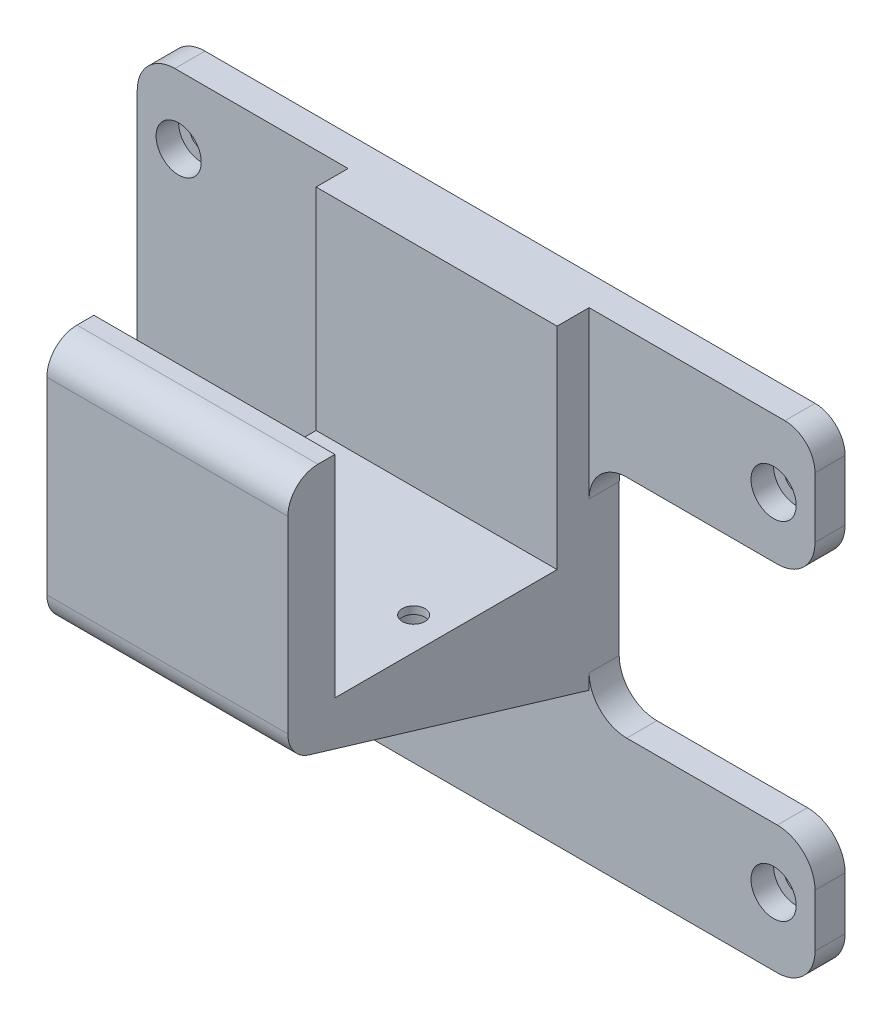
SolidWorks part; units mm, degrees
ref_plane "前视基准面" through (0, 0, 0) normal (0, 0, 1) x (1, 0, 0)
ref_plane "上视基准面" through (0, 0, 0) normal (0, 1, 0) x (1, 0, 0)
ref_plane "右视基准面" through (0, 0, 0) normal (1, 0, 0) x (0, 0, -1)
sketch "草图1" plane through (0, 0, 0) normal (0, 0, 1) x (1, 0, 0)
  line L0 (0, 0) -> (44.2288, 0) construction
  line L1 (-40, 32) -> (41, 32)
  line L2 (-45, 27) -> (-45, -27)
  line L3 (-40, -32) -> (40, -32)
  line L5 (-45, 32) -> (45, -32) construction
  line L6 (-45, -32) -> (45, 32) construction
  line L7 (0, 0) -> (0, 17.8738) construction
  line L8 (45, -20) -> (45, -27)
  line L9 (40, 15) -> (20, 15)
  line L11 (40, -15) -> (20, -15)
  line L12 (15, 10) -> (15, -10)
  line L13 (45, 28) -> (45, 20)
  arc A1 (40, -32) -> (45, -27) centre (40, -27) ccw
  arc A2 (-45, -27) -> (-40, -32) centre (-40, -27) ccw
  arc A3 (-40, 32) -> (-45, 27) centre (-40, 27) ccw
  circle A4 centre (-39.5, 23) radius 1.5
  circle A5 centre (-39.5, -23) radius 1.5
  circle A6 centre (39.5, -23) radius 1.5
  circle A7 centre (39.5, 23) radius 1.5
  arc A8 (45, -20) -> (40, -15) centre (40, -20) ccw
  arc A9 (20, -15) -> (15, -10) centre (20, -10) cw
  arc A10 (20, 15) -> (15, 10) centre (20, 10) ccw
  arc A11 (40, 15) -> (45, 20) centre (40, 20) ccw
  arc A12 (41, 32) -> (45, 28) centre (41, 28) cw
  point P39 (15, 15)
  point P42 (45, 15)
  dimension "D3" = 4
  dimension "D4" = 46
  dimension "D9" = 5
  dimension "D1" = 64
  dimension "D2" = 90
  dimension "D6" = 15
  dimension "D7" = 15
  dimension "D8" = 30
extrude "凸台-拉伸1" add sketch "草图1" along normal blind 4
sketch "草图2" plane through (0, 0, 4) normal (0, 0, 1) x (1, 0, 0)
  line L0 (0, 0) -> (-52.5196, 0) construction
  line L1 (0, 0) -> (0, 42.2378) construction
  circle A0 centre (-39.5, 23) radius 3
  circle A1 centre (-39.5, -23) radius 3
  circle A2 centre (39.5, -23) radius 3
  circle A3 centre (39.5, 23) radius 3
extrude "切除-拉伸1" cut sketch "草图2" against normal blind 3
sketch "草图3" plane through (0, 0, 4) normal (0, 0, 1) x (1, 0, 0)
  line L1 (-17, 32) -> (15, 32)
  line L2 (-17, 32) -> (-17, -12)
  line L3 (-17, -12) -> (15, -12)
  line L4 (15, 32) -> (15, -12)
  line L9 (15, -10) -> (15, 10) construction
  line L10 (41, 32) -> (-40, 32) construction
  dimension "D1" = 32
extrude "凸台-拉伸2" add sketch "草图3" along normal blind 40
sketch "草图4" plane through (0, 32, 0) normal (0, 1, 0) x (1, 0, 0)
  line L0 (-15, -23) -> (19.2476, -23) construction
  line L1 (-17, -44) -> (-17, -4) construction
  circle A0 centre (-13, -13) radius 1.5
  circle A1 centre (-13, -33) radius 1.5
  circle A2 centre (10.7, -23) radius 1.5
  dimension "D1" = 20
  dimension "D2" = 23.7
  dimension "D3" = 4
extrude "切除-拉伸2" cut sketch "草图4" against normal through all
sketch "草图5" plane through (0, -12, 0) normal (0, -1, 0) x (1, 0, 0)
  circle A0 centre (-13, 33) radius 3
  circle A1 centre (-13, 13) radius 3
  circle A2 centre (10.7, 23) radius 3
extrude "切除-拉伸10" cut sketch "草图5" against normal blind 15
sketch "草图7" plane through (0, 32, 0) normal (0, 1, 0) x (1, 0, 0)
  line L0 (-17, -44) -> (-17, -4) construction
  line L1 (-17, -8.25) -> (15, -8.25)
  line L2 (-17, -8.25) -> (-17, -37.75)
  line L3 (-17, -37.75) -> (15, -37.75)
  line L4 (15, -8.25) -> (15, -37.75)
  line L5 (15, -44) -> (15, -4) construction
  line L6 (10.7, -23) -> (-18.4544, -23) construction
  line L7 (-17, -4) -> (-40, -4) construction
  dimension "D1" = 4.25
extrude "切除-拉伸12" cut sketch "草图7" against normal blind 28
sketch "草图6" plane through (-17, 0, 0) normal (-1, 0, 0) x (0, 0, 1)
  line L0 (44, 32) -> (44, -12) construction
  line L10 (8.25, 4) -> (37.75, 4) construction
  line L11 (4, -12) -> (41.1494, -0.8552)
  line L12 (40, 32) -> (44, 32)
  line L17 (44, 32) -> (44, 28)
  line L18 (4, -12) -> (44, -12)
  line L19 (44, -12) -> (44, 2.9761)
  arc A2 (40, 32) -> (44, 28) centre (40, 28) cw
  arc A3 (41.1494, -0.8552) -> (44, 2.9761) centre (40, 2.9761) ccw
  point P0 (44, 0)
  dimension "D2" = 4
  dimension "D3" = 4
  dimension "D1" = 4
extrude "切除-拉伸11" cut sketch "草图6" against normal through all
